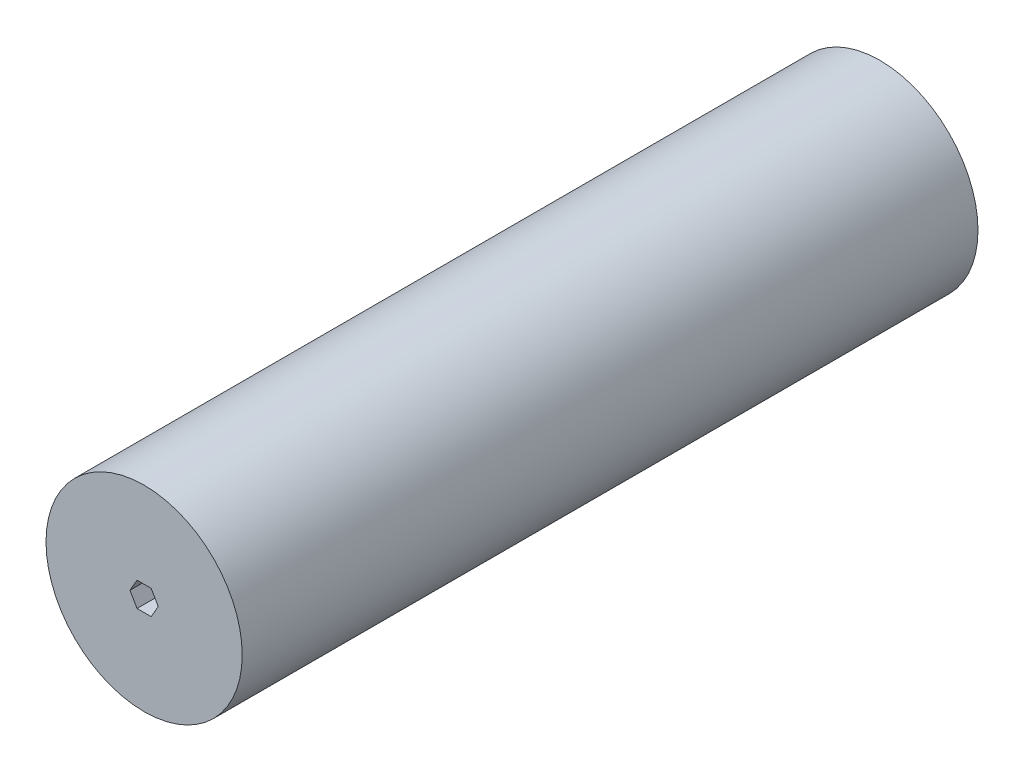
SolidWorks part; units mm, degrees
ref_plane "Front Plane" through (0, 0, 0) normal (0, 0, 1) x (1, 0, 0)
ref_plane "Top Plane" through (0, 0, 0) normal (0, 1, 0) x (1, 0, 0)
ref_plane "Right Plane" through (0, 0, 0) normal (1, 0, 0) x (0, 0, -1)
sketch "Sketch1" plane through (0, 0, 0) normal (0, 0, 1) x (1, 0, 0)
  circle A0 centre (0, 0) radius 50.8
  dimension "D1" = 101.6
extrude "Boss-Extrude1" add sketch "Sketch1" along normal blind 381
sketch "Sketch2" plane through (0, 0, 381) normal (0, 0, 1) x (1, 0, 0)
  line L1 (3.6662, 6.35) -> (-3.6662, 6.35)
  line L2 (-3.6662, 6.35) -> (-7.3323, 0)
  line L3 (-7.3323, 0) -> (-3.6662, -6.35)
  line L4 (-3.6662, -6.35) -> (3.6662, -6.35)
  line L5 (3.6662, -6.35) -> (7.3323, 0)
  line L6 (7.3323, 0) -> (3.6662, 6.35)
  circle A0 centre (0, 0) radius 6.35 construction
  dimension "D1" = 12.7
extrude "Cut-Extrude1" cut sketch "Sketch2" against normal through all both and the other way through all
